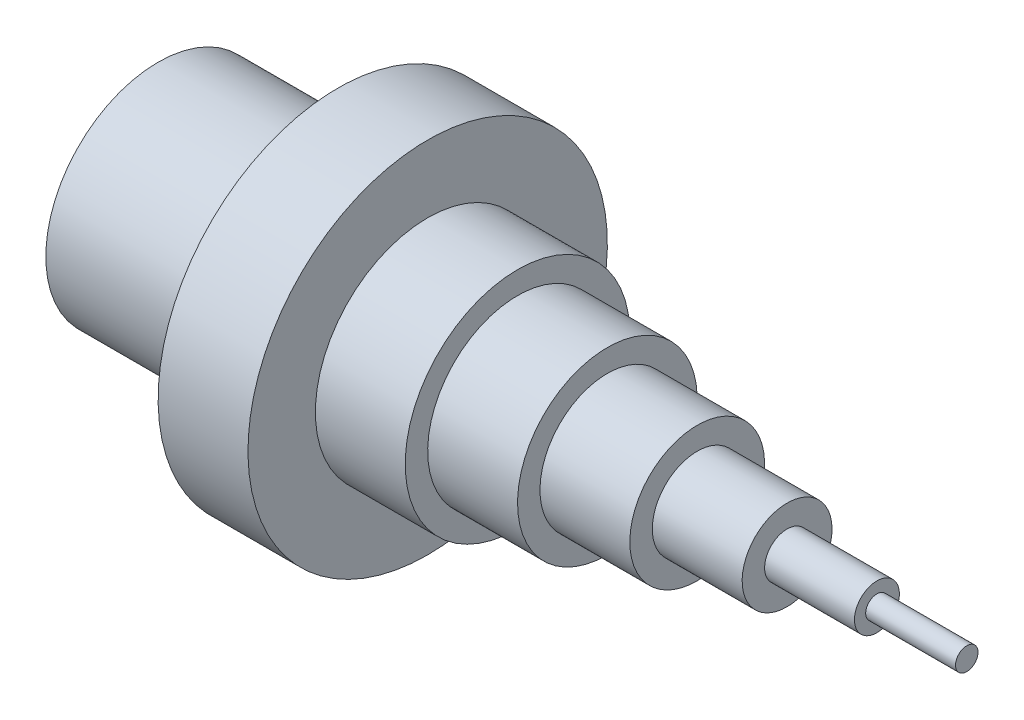
SolidWorks part; units mm, degrees
ref_plane "Front Plane" through (0, 0, 0) normal (0, 0, 1) x (1, 0, 0)
ref_plane "Top Plane" through (0, 0, 0) normal (0, 1, 0) x (1, 0, 0)
ref_plane "Right Plane" through (0, 0, 0) normal (1, 0, 0) x (0, 0, -1)
sketch "Sketch1" plane through (0, 0, 0) normal (0, 0, 1) x (1, 0, 0)
  line L0 (-272.6482, 0) -> (272.6482, 0) construction
  line L1 (0, 0) -> (0, 25)
  line L2 (0, 25) -> (40, 25)
  line L3 (40, 25) -> (40, 40)
  line L4 (40, 40) -> (60, 40)
  line L5 (60, 40) -> (60, 25)
  line L6 (60, 25) -> (80, 25)
  line L7 (80, 25) -> (80, 20)
  line L8 (80, 20) -> (100, 20)
  line L9 (100, 20) -> (100, 15)
  line L10 (100, 15) -> (120, 15)
  line L11 (120, 15) -> (120, 10)
  line L12 (120, 10) -> (140, 10)
  line L13 (140, 10) -> (140, 5)
  line L14 (140, 5) -> (160, 5)
  line L15 (160, 5) -> (160, 2.5)
  line L16 (160, 2.5) -> (180, 2.5)
  line L17 (180, 2.5) -> (180, 0)
  line L18 (180, 0) -> (0, 0)
  point P4 (0, 0)
  dimension "D1" = 40
  dimension "D2" = 50
  dimension "D3" = 80
  dimension "D4" = 50
  dimension "D5" = 40
  dimension "D6" = 30
  dimension "D7" = 20
  dimension "D8" = 10
  dimension "D9" = 5
  dimension "D10" = 20
  dimension "D11" = 180
revolve "Revolve1" add sketch "Sketch1" angle 360 about L0
sketch "Sketch2" plane through (0, 0, 0) normal (-1, 0, 0) x (0, 0, 1)
  circle A0 centre (0, 0) radius 20
  dimension "D1" = 40
extrude "Cut-Extrude2" cut sketch "Sketch2" against normal up to surface (40 mm away) contours A0 up to face at (40, -25, 0)
